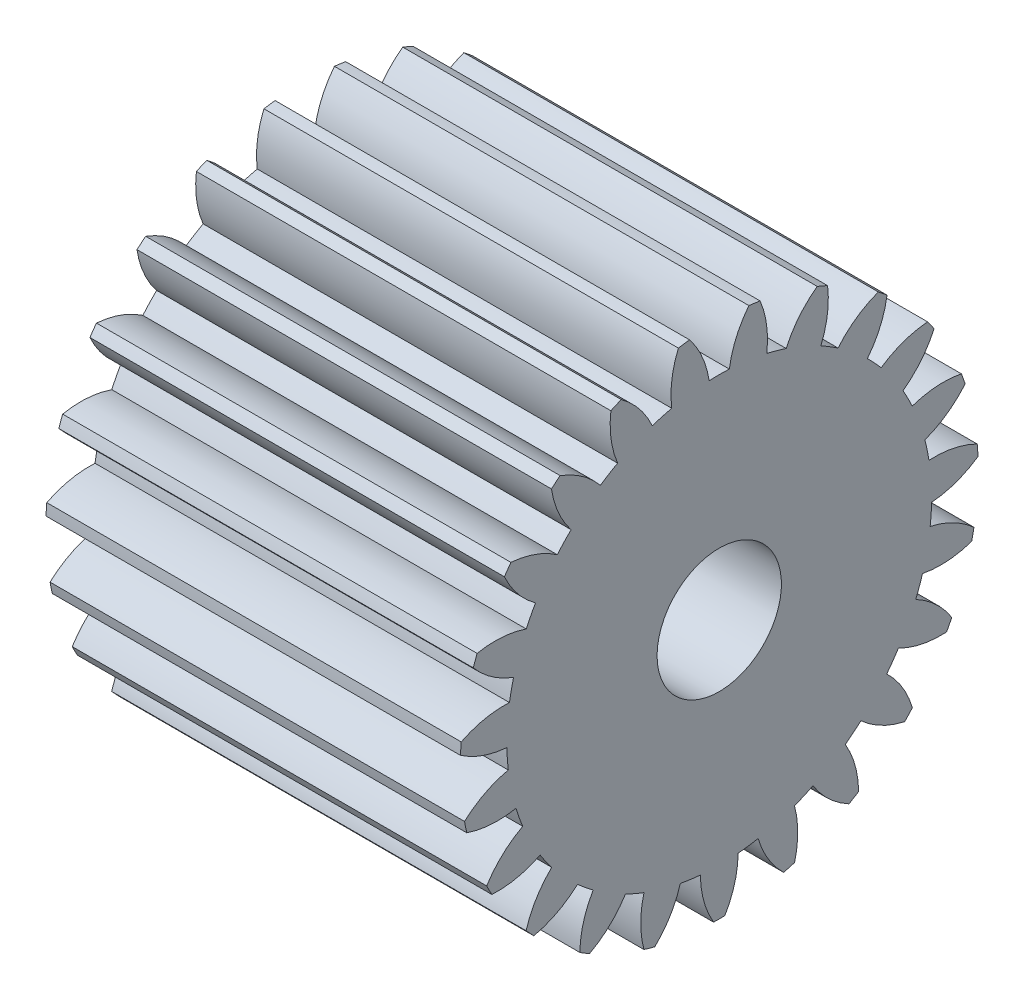
SolidWorks part; units mm, degrees
material "1.0035 (S185)"
ref_plane "Plane1" through (0, 0, 0) normal (0, 0, 1) x (1, 0, 0)
ref_plane "Plane2" through (0, 0, 0) normal (0, 1, 0) x (1, 0, 0)
ref_plane "Plane3" through (0, 0, 0) normal (1, 0, 0) x (0, 0, -1)
sketch "HoldingSke" plane through (0, 0, 0) normal (0, 1, 0) x (1, 0, 0)
  line L0 (0, 0) -> (1.841, -0.7815)
  line L1 (-15, 0) -> (100, 0) construction
  line L2 (0, 0) -> (-2.1039, 2.3779)
  line L3 (0, 0) -> (-11.863, 4.5341)
  line L4 (0, 0) -> (7.9495, 3.3744)
  line L5 (0, 0) -> (-46.8476, -17.4728)
  line L6 (0, 0) -> (-8.2896, -5.593)
  line L7 (-2.1039, 2.3779) -> (8.6586, 51.2059)
  line L8 (-76.2, 54.61) -> (-75.7, 54.61)
  line L9 (-71.009, 38.7566) -> (-53.1078, 45.2721)
  line L10 (-76.2, 71.12) -> (104.1128, 71.12)
  line L11 (0, 0) -> (-10, 0)
  line L12 (-76.2, 101.6) -> (-76.181, 101.6)
  line L13 (24.9733, 27.94) -> (52.9518, 28.4284)
  line L14 (24.9733, 27.94) -> (24.9743, 27.94)
  line L15 (24.9733, 27.94) -> (100.4006, 29.5858)
  line L16 (-63.627, -0.5) -> (-12.827, -0.5)
  circle A0 centre (0, 0) radius 1.5
  circle A1 centre (0, 0) radius 5.124
  circle A2 centre (0, 0) radius 37.5
  circle A3 centre (0, 0) radius 1.5
  dimension "MHD" = 10.248
  dimension "Hub_dia" = 75
  dimension "Bore" = 3
  dimension "MBD" = 3
  dimension "Num_teeth" = 23
  dimension "Pitch_radius" = 180.3128
  dimension "Pitch" = 2
  dimension "Width" = 10
  dimension "Overall_len" = 50
  dimension "Show_teeth" = 23
  dimension "Thickness" = 10
  dimension "OAL" = 50.0001
  dimension "T_dim" = 0.5
  dimension "Ap" = 20
  dimension "H" = 19.05
  dimension "Backlash" = 0.019
  dimension "Addendum_fac" = 1
  dimension "Dedendum_fac" = 1.25
  dimension "Clearance_fac" = 0.25
  dimension "Dedendum_add" = 0.001
  dimension "Module" = 0.5
sketch "BasProSke" plane through (0, 0, 0) normal (0, 1, 0) x (1, 0, 0)
  line L0 (-10, 0) -> (60, 0) construction
  line L1 (0, 0) -> (0, 6.25)
  line L2 (0, 0) -> (10, 0)
  line L3 (10, 0) -> (10, 6.25)
  line L4 (10, 6.25) -> (0, 6.25)
  dimension "Diameter" = 12.5
  dimension "Thickness" = 10
revolve "Base-Revolve" add sketch "BasProSke" angle 360 about L0
sketch "TooCutSke" plane through (0, 0, 0) normal (1, 0, 0) x (0, 0, -1)
  line L1 (0, 0) -> (0, 107) construction
  line L2 (0, 0) -> (-0.4256, 5.7342) construction
  line L3 (0, 0) -> (-1.5629, 11.3706) construction
  line L4 (-0.4256, 5.7342) -> (-0.7814, 5.6853) construction
  arc A0 (0.2435, 5.1182) -> (-0.2435, 5.1182) centre (0, 0) ccw
  arc A1 (0.7347, 6.2322) -> (-0.7347, 6.2322) centre (0, 0) ccw
  circle A2 centre (0, 0) radius 5.75 construction
  circle A3 centre (0, 0) radius 5.4032 construction
  arc A4 (-0.2435, 5.1182) -> (-0.7347, 6.2322) centre (-2.5185, 4.7804) ccw
  arc A5 (0.7347, 6.2322) -> (0.2435, 5.1182) centre (2.5185, 4.7804) ccw
  dimension "Root_dia" = 10.248
  dimension "Overcut_dia" = 12.5508
  dimension "Pitch_dia" = 11.5
  dimension "Base_dia" = 10.8065
  dimension "Flank_rad" = 2.3
  dimension "Half_ang" = 7.826
  dimension "Half_CT" = 0.3591
extrude "ToothCut" cut sketch "TooCutSke" along normal through all
fillet "Breaks" [suppressed] radius 0.01
fillet "RootFillets" [suppressed] radius 0.126
pattern_circular "TeethCuts" count 23 every 15.652 about axis through (-10, 0, 0) along (1, 0, 0) of "ToothCut", "RootFillets", "Breaks"
sketch "HubNeaOneSke" plane through (0, 0, 0) normal (-1, 0, 0) x (0, 0, 1)
  circle A0 centre (0, 0) radius 5.124
  dimension "Diameter" = 10.248
extrude "HubNearOne" [suppressed] add sketch "HubNeaOneSke" along normal blind 40.0001
sketch "HubNeaBotSke" plane through (0, 0, 0) normal (-1, 0, 0) x (0, 0, 1)
  circle A0 centre (0, 0) radius 5.124
  dimension "Diameter" = 10.248
extrude "HubNearBoth" [suppressed] add sketch "HubNeaBotSke" along normal blind 20
ref_plane "FarPln" through (10, 0, 0) normal (1, 0, 0) x (0, 0, -1)
sketch "HubFarSke" plane through (10, 0, 0) normal (1, 0, 0) x (0, 0, -1)
  circle A0 centre (0, 0) radius 5.124
  dimension "Diameter" = 10.248
extrude "HubFar" [suppressed] add sketch "HubFarSke" along normal blind 20
sketch "BorSke" plane through (0, 0, 0) normal (1, 0, 0) x (0, 0, -1)
  circle A0 centre (0, 0) radius 1.5
  dimension "Diameter" = 3
extrude "Bore" cut sketch "BorSke" along normal mid plane 100.0001
sketch "KeySke" plane through (0, 0, 0) normal (1, 0, 0) x (0, 0, -1)
  line L0 (-0.6, 0) -> (-0.6, 2)
  line L1 (-0.6, 2) -> (0.6, 2)
  line L2 (0.6, 2) -> (0.6, 0)
  line L3 (0, 0) -> (0, 34) construction
  line L4 (-0.6, 0) -> (0.6, 0)
  dimension "Offset" = 2
  dimension "Width" = 1.2
extrude "Keyway" [suppressed] cut sketch "KeySke" along normal mid plane 100.0001
pattern_circular "Keyway2" [suppressed] count 2 every 90 about axis through (-10, 0, 0) along (1, 0, 0)
equation "' \"Module@HoldingSke\" = 6.35"
equation "' \"Num_teeth@HoldingSke\" = 12"
equation "' \"Ap@HoldingSke\" =  20"
equation "' \"Width@HoldingSke\" = 0.5 * 25.4"
equation "' \"Hub_dia@HoldingSke\"= 1 * 25.4"
equation "' \"Overall_len@HoldingSke\" = 1.0 * 25.4"
equation "' \"Bore@HoldingSke\" = 0.75 * 25.4"
equation "' \"T_dim@HoldingSke\" = 0.1 * 25.4"
equation "' \"Width@KeySke\" = 0.25 * 25.4"
equation "' \"Show_teeth@HoldingSke\" = 13"
equation "' \"Backlash@HoldingSke\" = 0.009 * 25.4"
equation "' \"Addendum_fac@HoldingSke\" = 1.0"
equation "' \"Dedendum_fac@HoldingSke\" = 1.25"
equation "' \"Dedendum_add@HoldingSke\" = 0.00005 * 25.4"
equation "' \"Clearance_fac@HoldingSke\" = 0.25"
equation "\"Pitch@HoldingSke\" = 1 / \"Module@HoldingSke\""
equation "\"Overcut_dia@TooCutSke\" = (\"Num_teeth@HoldingSke\" + 2 * \"Addendum_fac@HoldingSke\") / \"Pitch@HoldingSke\" + 0.002 * 25.4"
equation "\"Pitch_dia@TooCutSke\" = \"Num_teeth@HoldingSke\" / \"Pitch@HoldingSke\""
equation "\"Base_dia@TooCutSke\" = \"Num_teeth@HoldingSke\" / \"Pitch@HoldingSke\" * cos((\"Ap@HoldingSke\"  * 3.14159265 / 180))"
equation "\"Root_dia@TooCutSke\" = (\"Num_teeth@HoldingSke\" + 2) / \"Pitch@HoldingSke\" - 2 * (\"Addendum_fac@HoldingSke\" + \"Dedendum_fac@HoldingSke\") / \"Pitch@HoldingSke\" - \"Dedendum_add@HoldingSke\" * 2"
equation "\"Half_ang@TooCutSke\" = 180 / \"Num_teeth@HoldingSke\""
equation "\"Half_CT@TooCutSke\" = \"Num_teeth@HoldingSke\" / \"Pitch@HoldingSke\" * sin((3.14159265 / 2 / \"Num_teeth@HoldingSke\")) / 2 - 7 * \"Backlash@HoldingSke\" / 4"
equation "\"Flank_rad@TooCutSke\" = \"Num_teeth@HoldingSke\" / \"Pitch@HoldingSke\" / 5"
equation "\"Radius@RootFillets\" = \"Clearance_fac@HoldingSke\" / \"Pitch@HoldingSke\" + \"Dedendum_add@HoldingSke\""
equation "\"Break_rad@Breaks\" = 0.02 / \"Pitch@HoldingSke\""
equation "\"Thickness@HoldingSke\" = \"Width@HoldingSke\""
equation "\"OAL@HoldingSke\" = \"Thickness@HoldingSke\""
equation "\"MHD@HoldingSke\" = (\"Num_teeth@HoldingSke\" + 2) / \"Pitch@HoldingSke\" - 2 * (\"Addendum_fac@HoldingSke\" + \"Dedendum_fac@HoldingSke\")  / \"Pitch@HoldingSke\" - \"Dedendum_add@HoldingSke\" * 2"
equation "\"MBD@HoldingSke\" = (\"Num_teeth@HoldingSke\" + 2) / \"Pitch@HoldingSke\" - 2 * (\"Addendum_fac@HoldingSke\" + \"Dedendum_fac@HoldingSke\")  / \"Pitch@HoldingSke\" - \"Dedendum_add@HoldingSke\" * 2 - 0.002 * 25.4"
equation "\"MHD@HoldingSke\" = ((sgn( \"MHD@HoldingSke\" - \"Hub_dia@HoldingSke\" )-1)*( \"MHD@HoldingSke\" - \"Hub_dia@HoldingSke\" ))/-2+ \"Hub_dia@HoldingSke\""
equation "\"MBD@HoldingSke\" = ((sgn( \"MBD@HoldingSke\" - \"Bore@HoldingSke\" )-1)*( \"MBD@HoldingSke\" - \"Bore@HoldingSke\" ))/-2+ \"Bore@HoldingSke\""
equation "\"OAL@HoldingSke\" = ((sgn( \"OAL@HoldingSke\" - \"Overall_len@HoldingSke\" )+1)*( \"OAL@HoldingSke\" - \"Overall_len@HoldingSke\" ))/2 + \"Overall_len@HoldingSke\" + 0.000002 * 25.4"
equation "\"Num_teeth@TeethCuts\" = int( \"Show_teeth@HoldingSke\" ) + 1"
equation "\"Num_teeth@TeethCuts\" = ((sgn( \"Num_teeth@TeethCuts\" - \"Num_teeth@HoldingSke\" )-1)*( \"Num_teeth@TeethCuts\" - \"Num_teeth@HoldingSke\" ))/-2+ \"Num_teeth@HoldingSke\""
equation "\"Num_teeth@TeethCuts\" = ((sgn( \"Num_teeth@TeethCuts\" - 2.0)+1)*( \"Num_teeth@TeethCuts\" - 2.0))/2 +2.0"
equation "\"Angle@TeethCuts\" = 360.0 / \"Num_teeth@HoldingSke\""
equation "\"Diameter@BasProSke\" = (\"Num_teeth@HoldingSke\" + 2 * \"Addendum_fac@HoldingSke\") / \"Pitch@HoldingSke\""
equation "\"Thickness@BasProSke\"  = \"Thickness@HoldingSke\""
equation "' \"Fillet_rad@BasProSke\" =  \"Thickness@HoldingSke\" * 0.05"
equation "\"MHD@HoldingSke\" = ((sgn( \"MHD@HoldingSke\" - \"Root_dia@TooCutSke\" )-1)*( \"MHD@HoldingSke\" - \"Root_dia@TooCutSke\" ))/-2+ \"Root_dia@TooCutSke\""
equation "\"Diameter@HubNeaOneSke\" = \"MHD@HoldingSke\""
equation "\"Length@HubNearOne\" = \"OAL@HoldingSke\" - \"Thickness@BasProSke\""
equation "\"Diameter@HubNeaBotSke\" = \"MHD@HoldingSke\""
equation "\"Length@HubNearBoth\" = ( \"OAL@HoldingSke\" - \"Thickness@BasProSke\" ) / 2.0"
equation "\"Thickness@FarPln\" = \"Thickness@BasProSke\""
equation "\"Diameter@HubFarSke\" = \"MHD@HoldingSke\""
equation "\"Length@HubFar\" = ( \"OAL@HoldingSke\" - \"Thickness@BasProSke\" ) / 2.0"
equation "\"Diameter@BorSke\" = \"MBD@HoldingSke\""
equation "\"D1@Bore\" = \"OAL@HoldingSke\" * 2.0"
equation "\"D1@Keyway\" = \"OAL@HoldingSke\" * 2.0"
equation "\"Offset@KeySke\" = \"T_dim@HoldingSke\" + \"MBD@HoldingSke\" / 2.0"
